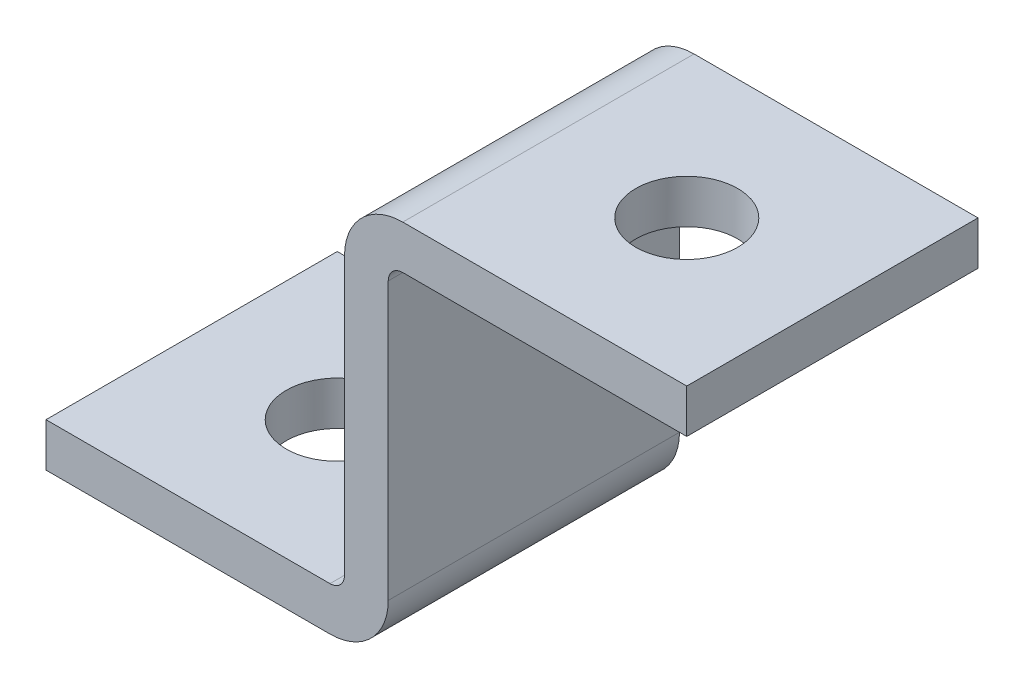
SolidWorks part; units mm, degrees
ref_plane "Front Plane" through (0, 0, 0) normal (0, 0, 1) x (1, 0, 0)
ref_plane "Top Plane" through (0, 0, 0) normal (0, 1, 0) x (1, 0, 0)
ref_plane "Right Plane" through (0, 0, 0) normal (1, 0, 0) x (0, 0, -1)
ref_plane "Plane1" through (0, 0, -40) normal (0, 0, -1) x (-1, 0, 0)
sketch "Sketch1" plane through (0, 0, -40) normal (0, 0, -1) x (-1, 0, 0)
  line L0 (-88, 54) -> (-88, 0)
  line L1 (-88, 0) -> (0, 0)
  line L2 (0, 0) -> (0, 54)
  line L3 (0, 54) -> (-88, 54)
extrude "Boss-Extrude1" add sketch "Sketch1" against normal blind 40
sketch "Sketch2" plane through (0, 0, 0) normal (0, 0, 1) x (1, 0, 0)
  line L0 (41, 6) -> (41, 54)
  line L1 (41, 54) -> (0, 54)
  line L2 (0, 54) -> (0, 6)
  line L3 (0, 6) -> (41, 6)
extrude "Cut-Extrude1" cut sketch "Sketch2" against normal through all
sketch "Sketch3" plane through (0, 0, 0) normal (0, 0, 1) x (1, 0, 0)
  line L0 (88, 48) -> (47, 48)
  line L1 (47, 48) -> (47, 0)
  line L2 (47, 0) -> (88, 0)
  line L3 (88, 0) -> (88, 48)
extrude "Cut-Extrude2" cut sketch "Sketch3" against normal through all
hole_wizard "Ø14.0 (14) Diameter Hole1" positions "Sketch5" profile "Sketch4" hole size "Ø14.0" standard "ANSI Metric"
sketch "Sketch5" plane through (0, 0, 0) normal (0, -1, 0) x (-1, 0, 0)
  point P0 (-20, 20)
sketch "Sketch4" plane through (20, 0, -20) normal (1, 0, 0) x (0, 0, -1)
  line L0 (0, 0) -> (0, 54)
  line L1 (0, 54) -> (7, 54)
  line L2 (7, 54) -> (7, 0)
  line L5 (7, 0) -> (0, 0)
  line L11 (0, -6.35) -> (0, 107.95) construction
  dimension "Thru Hole Dia." = 14
  dimension "Thru Hole Depth" = 54
hole_wizard "Ø14.0 (14) Diameter Hole2" positions "Sketch7" profile "Sketch6" hole size "Ø14.0" standard "ANSI Metric"
sketch "Sketch7" plane through (0, 54, 0) normal (0, 1, 0) x (1, 0, 0)
  point P0 (68, 20)
sketch "Sketch6" plane through (68, 54, -20) normal (1, 0, 0) x (0, 0, 1)
  line L0 (0, 0) -> (0, 54)
  line L1 (0, 54) -> (7, 54)
  line L2 (7, 54) -> (7, 0)
  line L5 (7, 0) -> (0, 0)
  line L11 (0, -6.35) -> (0, 107.95) construction
  dimension "Thru Hole Dia." = 14
  dimension "Thru Hole Depth" = 54
fillet "Fillet1" radius 2 2 edges at (47, 48, -20) (41, 6, -20)
fillet "Fillet2" radius 8 2 edges at (47, 0, -20) (41, 54, -20)
